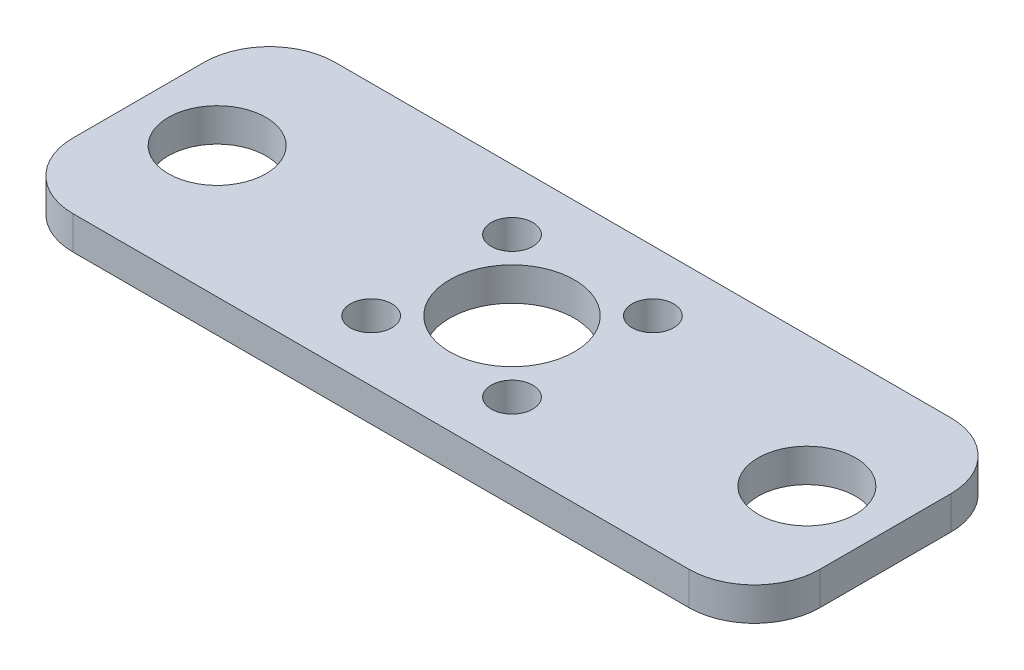
SolidWorks part; units mm, degrees
ref_plane "Front Plane" through (0, 0, 0) normal (0, 0, 1) x (1, 0, 0)
ref_plane "Top Plane" through (0, 0, 0) normal (0, 1, 0) x (1, 0, 0)
ref_plane "Right Plane" through (0, 0, 0) normal (1, 0, 0) x (0, 0, -1)
sketch "Sketch1" plane through (0, 0, 0) normal (0, 1, 0) x (1, 0, 0)
  line L0 (0, 20) -> (0, -20) construction
  line L1 (57, -20) -> (-57, -20)
  line L2 (57, -20) -> (57, 20)
  line L3 (57, 20) -> (-57, 20)
  line L4 (-57, -20) -> (-57, 20)
  line L5 (57, -20) -> (-57, 20) construction
  line L6 (57, 20) -> (-57, -20) construction
  circle A0 centre (-45, 0) radius 7.45
  circle A1 centre (45, 0) radius 7.45
  circle A2 centre (0, 0) radius 9.525
  point P0 (0, 0)
  dimension "D3" = 19.05
  dimension "D4" = 14.9
  dimension "D5" = 90
  dimension "D1" = 40
  dimension "D2" = 114
extrude "Boss-Extrude1" add sketch "Sketch1" along normal blind 5.08
fillet "Fillet1" radius 10 4 edges at (57, 2.54, -20) (57, 2.54, 20) (-57, 2.54, -20) (-57, 2.54, 20)
sketch "Sketch2" plane through (0, 5.08, 0) normal (0, 1, 0) x (1, 0, 0)
  line L1 (10.75, -10.75) -> (-10.75, -10.75) construction
  line L2 (10.75, -10.75) -> (10.75, 10.75) construction
  line L3 (10.75, 10.75) -> (-10.75, 10.75) construction
  line L4 (-10.75, -10.75) -> (-10.75, 10.75) construction
  line L5 (10.75, -10.75) -> (-10.75, 10.75) construction
  line L6 (10.75, 10.75) -> (-10.75, -10.75) construction
  circle A1 centre (0, 0) radius 9.525 construction
  circle A2 centre (-10.75, -10.75) radius 3.175
  circle A3 centre (-10.75, 10.75) radius 3.175
  circle A4 centre (10.75, 10.75) radius 3.175
  circle A5 centre (10.75, -10.75) radius 3.175
  point P0 (0, 0)
  dimension "D2" = 6.35
  dimension "D1" = 21.5
extrude "Cut-Extrude1" cut sketch "Sketch2" against normal through all
